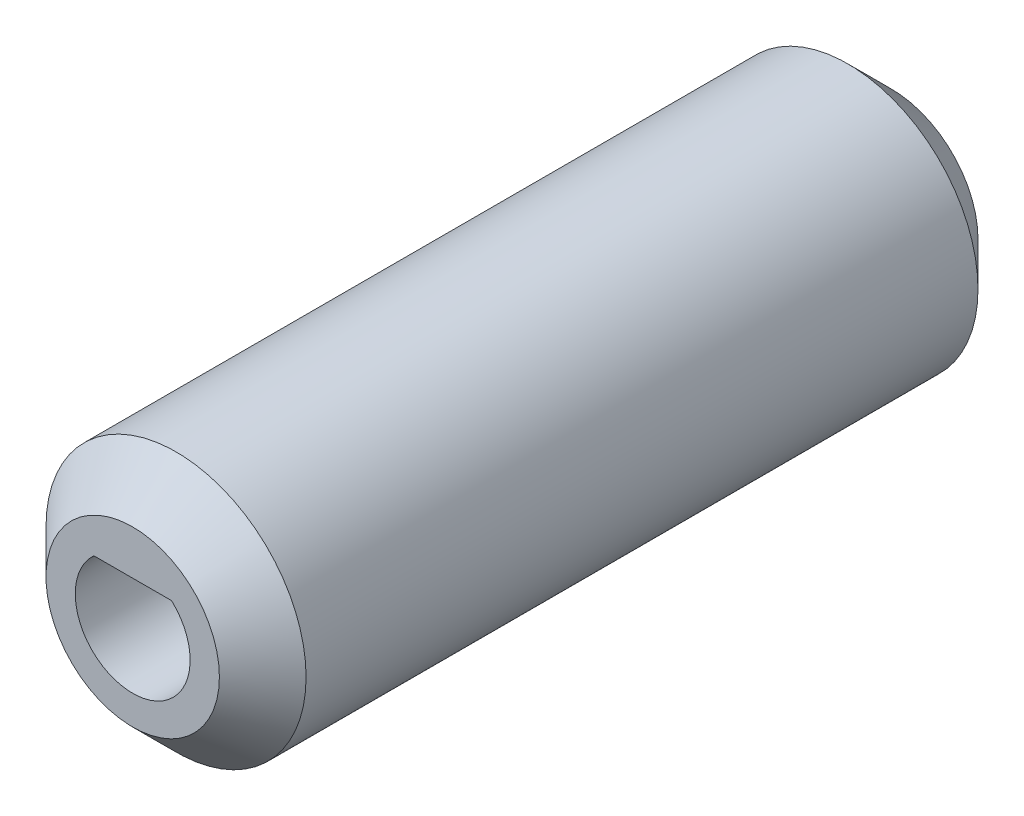
SolidWorks part; units mm, degrees
ref_plane "Front Plane" through (0, 0, 0) normal (0, 0, 1) x (1, 0, 0)
ref_plane "Top Plane" through (0, 0, 0) normal (0, 1, 0) x (1, 0, 0)
ref_plane "Right Plane" through (0, 0, 0) normal (1, 0, 0) x (0, 0, -1)
sketch "Sketch1" plane through (0, 0, 0) normal (0, 0, 1) x (1, 0, 0)
  circle A0 centre (0, 0) radius 6
  circle A1 centre (0, 0) radius 2.65
  dimension "D1" = 5.3
  dimension "D2" = 12
extrude "Boss-Extrude1" add sketch "Sketch1" along normal blind 35
sketch "Sketch2" plane through (0, 0, 35) normal (0, 0, 1) x (1, 0, 0)
  line L0 (-1.7944, 1.95) -> (1.7944, 1.95)
  circle A0 centre (0, 0) radius 2.65 construction
  circle A1 centre (0, 0) radius 2.65
  circle M4 centre (0, 0) radius 2.65
  dimension "D1" = 4.6
extrude "Boss-Extrude2" add sketch "Sketch2" against normal up to surface (35 mm away) contours L0 M4
chamfer "Chamfer1" distance 2 angle 45 2 edges at (6, 0, 0) (6, 0, 35)
